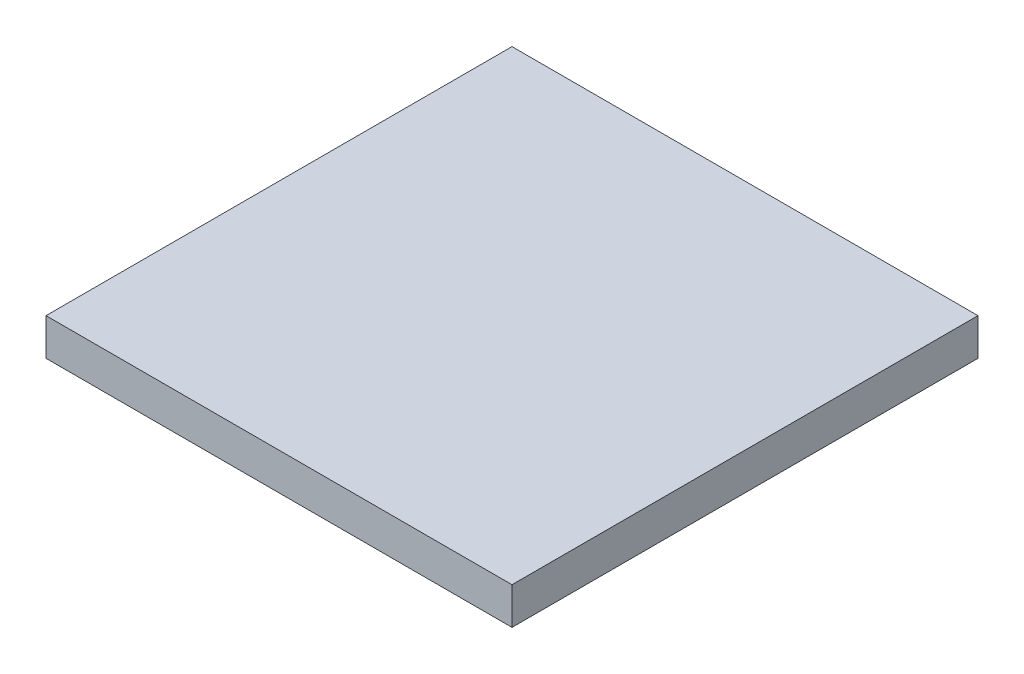
SolidWorks part; units mm, degrees
ref_plane "Front Plane" through (0, 0, 0) normal (0, 0, 1) x (1, 0, 0)
ref_plane "Top Plane" through (0, 0, 0) normal (0, 1, 0) x (1, 0, 0)
ref_plane "Right Plane" through (0, 0, 0) normal (1, 0, 0) x (0, 0, -1)
sketch "Sketch1" plane through (0, 0, 0) normal (0, 1, 0) x (1, 0, 0)
  line L1 (0, 0) -> (80.01, 0)
  line L2 (0, 0) -> (0, -80.01)
  line L3 (0, -80.01) -> (80.01, -80.01)
  line L4 (80.01, 0) -> (80.01, -80.01)
  dimension "D1" = 80.01
  dimension "D2" = 80.01
extrude "Boss-Extrude1" add sketch "Sketch1" along normal blind 6.35
